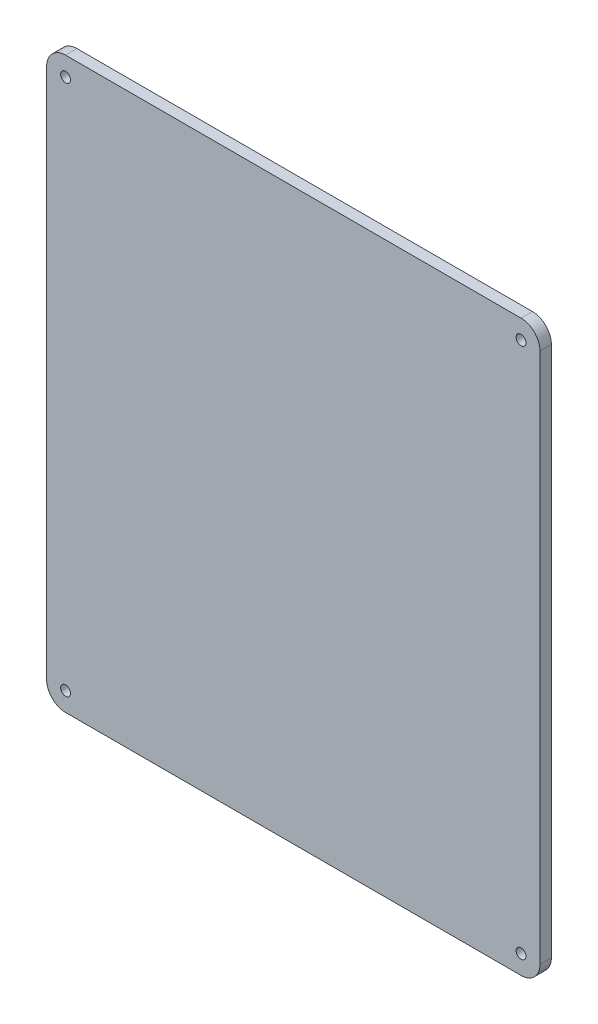
SolidWorks part; units mm, degrees
ref_plane "正面" through (0, 0, 0) normal (0, 0, 1) x (1, 0, 0)
ref_plane "平面" through (0, 0, 0) normal (0, 1, 0) x (1, 0, 0)
ref_plane "右側面" through (0, 0, 0) normal (1, 0, 0) x (0, 0, -1)
sketch "ｽｹｯﾁ1" plane through (0, 0, 0) normal (0, 0, 1) x (1, 0, 0)
  line L1 (-60, 75) -> (60, 75)
  line L2 (-65, 70) -> (-65, -70)
  line L3 (-60, -75) -> (60, -75)
  line L4 (65, 70) -> (65, -70)
  line L5 (-65, 75) -> (65, -75) construction
  line L6 (-65, -75) -> (65, 75) construction
  arc A0 (-65, -70) -> (-60, -75) centre (-60, -70) ccw
  arc A1 (60, -75) -> (65, -70) centre (60, -70) ccw
  arc A2 (65, 70) -> (60, 75) centre (60, 70) ccw
  arc A3 (-65, 70) -> (-60, 75) centre (-60, 70) cw
  point P0 (0, 0)
  dimension "D3" = 5
  dimension "D1" = 150
  dimension "D2" = 130
extrude "ﾎﾞｽ - 押し出し3" add sketch "ｽｹｯﾁ1" along normal blind 3
sketch "ｽｹｯﾁ2" plane through (0, 0, 3) normal (0, 0, 1) x (1, 0, 0)
  line L1 (-60, 70) -> (60, 70)
  line L2 (-60, 70) -> (-60, -70)
  line L3 (-60, -70) -> (60, -70)
  line L4 (60, 70) -> (60, -70)
  line L5 (-60, 70) -> (60, -70) construction
  line L6 (-60, -70) -> (60, 70) construction
  circle A0 centre (-60, 70) radius 1.3
  circle A1 centre (60, 70) radius 1.3
  circle A2 centre (60, -70) radius 1.3
  circle A3 centre (-60, -70) radius 1.3
  point P0 (0, 0)
  dimension "D3" = 2.6
  dimension "D4" = 2.6
  dimension "D5" = 2.6
  dimension "D6" = 2.6
  dimension "D1" = 140
  dimension "D2" = 120
extrude "ｶｯﾄ - 押し出し1" cut sketch "ｽｹｯﾁ2" against normal blind 3 contours A0 | A1 | A2 | A3
